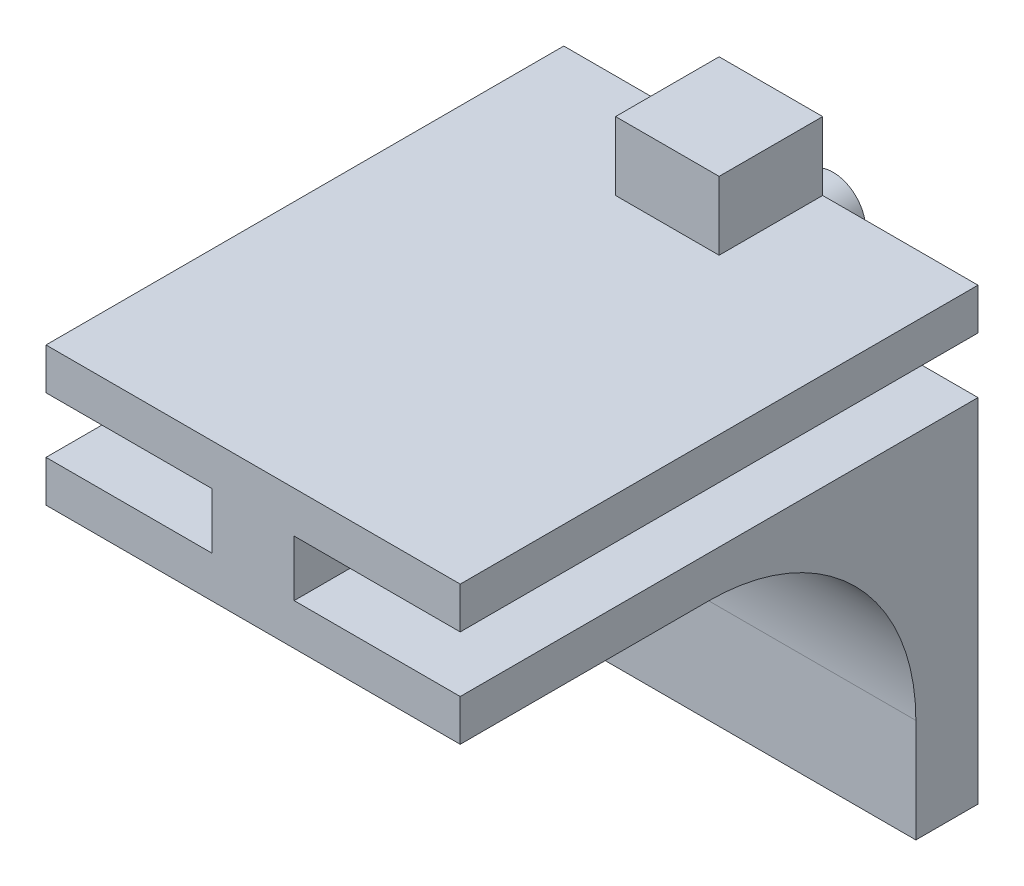
SolidWorks part; units mm, degrees
ref_plane "Front Plane" through (0, 0, 0) normal (0, 0, 1) x (1, 0, 0)
ref_plane "Top Plane" through (0, 0, 0) normal (0, 1, 0) x (1, 0, 0)
ref_plane "Right Plane" through (0, 0, 0) normal (1, 0, 0) x (0, 0, -1)
sketch "Sketch1" plane through (0, 0, 0) normal (0, 0, 1) x (1, 0, 0)
  line L0 (-49.3361, 0) -> (44.9688, 0) construction
  line L1 (0, 33.7475) -> (0, -43.3998) construction
  line L2 (10, -3.35) -> (-10, -3.35)
  line L3 (-10, -3.35) -> (-10, -1.35)
  line L4 (-10, -1.35) -> (-1.9812, -1.35)
  line L5 (-1.9812, -1.35) -> (-1.9812, 1.35)
  line L6 (-10, 1.35) -> (-1.9812, 1.35)
  line L7 (-10, 3.35) -> (-10, 1.35)
  line L8 (10, 3.35) -> (-10, 3.35)
  line L9 (10, 3.35) -> (10, 1.35)
  line L10 (10, 1.35) -> (1.9812, 1.35)
  line L11 (1.9812, -1.35) -> (1.9812, 1.35)
  line L12 (10, -1.35) -> (1.9812, -1.35)
  line L13 (10, -3.35) -> (10, -1.35)
  point P5 (1.9812, 0)
  point P11 (-1.9812, 0)
  point P15 (0, 3.35)
  point P20 (0, -3.35)
  dimension "D1" = 2.7
  dimension "D2" = 20
  dimension "D3" = 2
  dimension "D4" = 3.9624
extrude "Boss-Extrude1" add sketch "Sketch1" along normal blind 25
sketch "Sketch2" plane through (0, -3.35, 0) normal (0, -1, 0) x (1, 0, 0)
  line L0 (-10, 0) -> (-10, 3)
  line L1 (-10, 25) -> (-10, 0) construction
  line L2 (-10, 3) -> (10, 3)
  line L3 (10, 25) -> (10, 0) construction
  line L4 (10, 3) -> (10, 0)
  line L5 (10, 0) -> (-10, 0)
  dimension "D1" = 3
extrude "Boss-Extrude2" add sketch "Sketch2" along normal blind 15
fillet "Fillet1" radius 10 1 edges
sketch "Sketch3" plane through (0, 0, 0) normal (0, 0, -1) x (-1, 0, 0)
  circle A0 centre (0, 0) radius 1.5748
  dimension "D1" = 3.1496
extrude "Boss-Extrude3" add sketch "Sketch3" along normal blind 3
sketch "Sketch4" plane through (0, 3.35, 0) normal (0, 1, 0) x (1, 0, 0)
  line L0 (0, 8.4671) -> (0, -16.5621) construction
  line L1 (10, 0) -> (-10, 0) construction
  line L2 (-2.5, -5) -> (2.5, -5)
  line L3 (-2.5, -5) -> (-2.5, 0)
  line L4 (-2.5, 0) -> (2.5, 0)
  line L5 (2.5, -5) -> (2.5, 0)
  line L6 (-2.5, -5) -> (2.5, 0) construction
  line L7 (-2.5, 0) -> (2.5, -5) construction
  point P3 (0, -2.5)
  dimension "D1" = 5
  dimension "D2" = 5
extrude "Boss-Extrude4" add sketch "Sketch4" along normal blind 3.3
